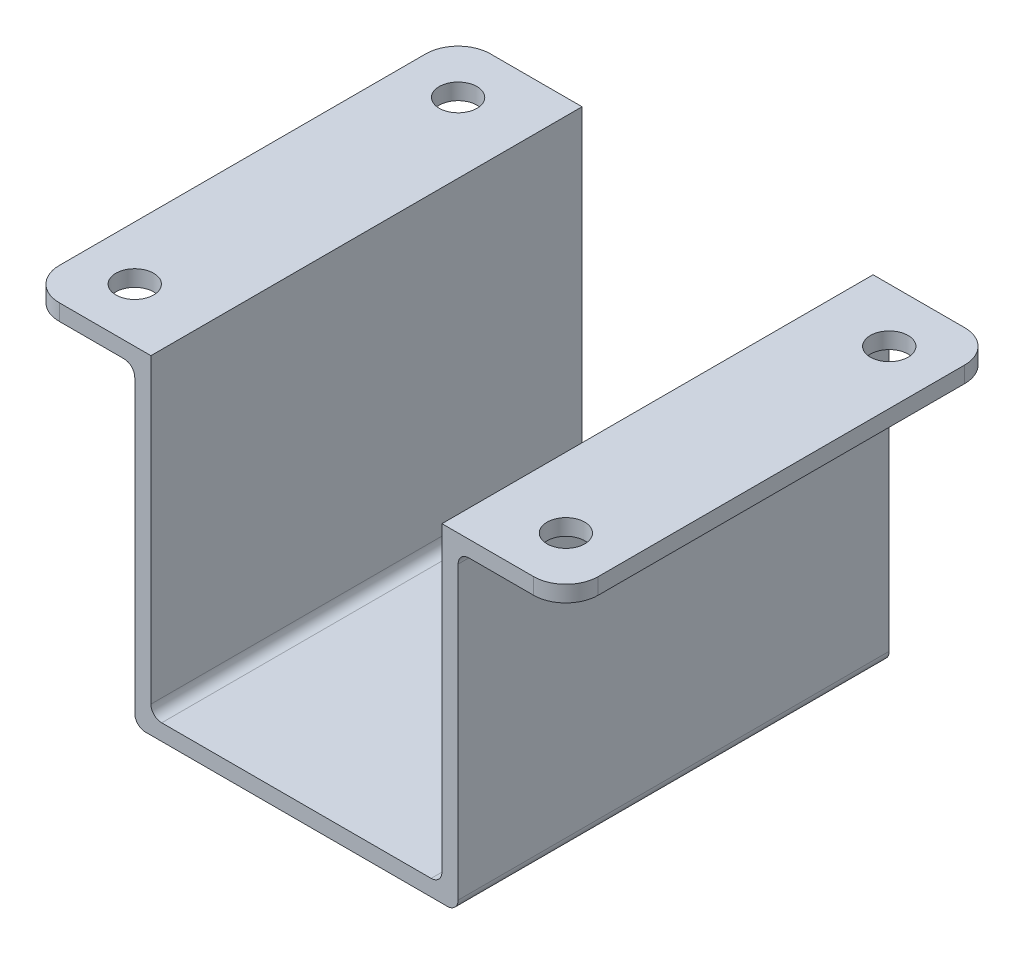
SolidWorks part; units mm, degrees
ref_plane "Front Plane" through (0, 0, 0) normal (0, 0, 1) x (1, 0, 0)
ref_plane "Top Plane" through (0, 0, 0) normal (0, 1, 0) x (1, 0, 0)
ref_plane "Right Plane" through (0, 0, 0) normal (1, 0, 0) x (0, 0, -1)
sketch "Sketch1" plane through (0, 0, 0) normal (0, 1, 0) x (1, 0, 0)
  line L1 (-15, 20) -> (15, 20)
  line L2 (-15, 20) -> (-15, -20)
  line L3 (-15, -20) -> (15, -20)
  line L4 (15, 20) -> (15, -20)
  circle A0 centre (0, 0) radius 4.25
extrude "Boss-Extrude1" add sketch "Sketch1" along normal blind 1.5
sketch "Sketch2" plane through (-15, 0, 0) normal (-1, 0, 0) x (0, 0, 1)
  line L1 (-20, 0) -> (20, 0)
  line L2 (-20, 0) -> (-20, 30.5)
  line L3 (-20, 30.5) -> (20, 30.5)
  line L4 (20, 0) -> (20, 30.5)
extrude "Boss-Extrude2" add sketch "Sketch2" against normal blind 1.5
sketch "Sketch3" plane through (0, 30.5, 0) normal (0, 1, 0) x (1, 0, 0)
  line L1 (-13.5, 20) -> (-25, 20)
  line L2 (-13.5, 20) -> (-13.5, -20)
  line L3 (-13.5, -20) -> (-25, -20)
  line L4 (-25, 20) -> (-25, -20)
  circle A0 centre (-20, 15) radius 1.75
  circle A1 centre (-20, -15) radius 1.75
  dimension "D1" = 2
extrude "Boss-Extrude3" add sketch "Sketch3" against normal blind 1.5
mirror "Mirror1" about plane through (0, 0, 0) normal (1, 0, 0) of "Boss-Extrude3", "Boss-Extrude2"
fillet "Fillet1" radius 1 6 edges at (15, 29, 0) (-15, 29, 0) (13.5, 1.5, 0) (-13.5, 1.5, 0) (15, 0, 0) (-15, 0, 0)
fillet "Fillet2" radius 3 4 edges at (-25, 29.75, -20) (25, 29.75, -20) (25, 29.75, 20) (-25, 29.75, 20)
equation "\"1.5.00mm\"=10"
